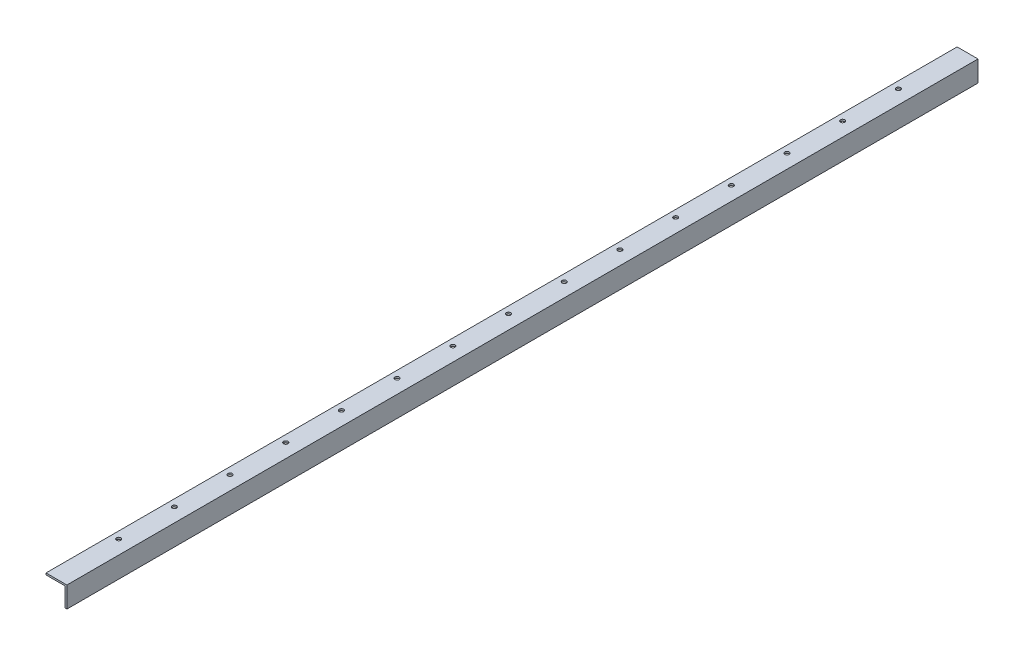
SolidWorks part; units mm, degrees
material "6063-T6"
ref_plane "Front Plane" through (0, 0, 0) normal (0, 0, 1) x (1, 0, 0)
ref_plane "Top Plane" through (0, 0, 0) normal (0, 1, 0) x (1, 0, 0)
ref_plane "Right Plane" through (0, 0, 0) normal (1, 0, 0) x (0, 0, -1)
sketch "Sketch1" plane through (0, 0, 0) normal (0, 0, 1) x (1, 0, 0)
  line L0 (0, 0) -> (-38.1, 0)
  line L1 (-38.1, 0) -> (-38.1, -3.175)
  line L2 (-38.1, -3.175) -> (-3.175, -3.175)
  line L3 (-3.175, -3.175) -> (-3.175, -38.1)
  line L4 (-3.175, -38.1) -> (0, -38.1)
  line L5 (0, -38.1) -> (0, 0)
  dimension "D1" = 38.1
  dimension "D2" = 3.175
extrude "Boss-Extrude1" add sketch "Sketch1" along normal blind 1662.1125
extrude "Cut-Extrude3" cut sketch "Sketch4" against normal blind 44.45
sketch "Sketch4" plane through (10.6701, 3.175, 817.757) normal (0, 1, 0) x (1, 0, 0)
  circle A0 centre (-36.0701, 697.9008) radius 3.9687
pattern_linear "LPattern1" count 15 spacing 101.6 along (0, 0, 1) of "Cut-Extrude3"
